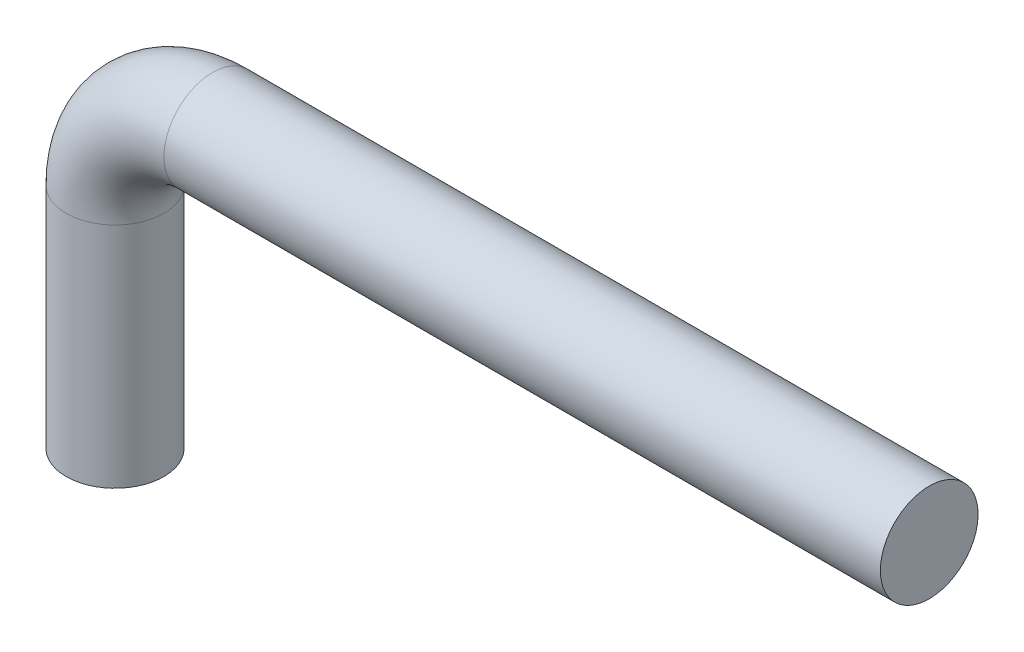
SolidWorks part; units mm, degrees
ref_plane "Front Plane" through (0, 0, 0) normal (0, 0, 1) x (1, 0, 0)
ref_plane "Top Plane" through (0, 0, 0) normal (0, 1, 0) x (1, 0, 0)
ref_plane "Right Plane" through (0, 0, 0) normal (1, 0, 0) x (0, 0, -1)
sketch "Sketch1" plane through (0, 0, 0) normal (0, 0, 1) x (1, 0, 0)
  line L0 (42.1927, 25.9485) -> (-13.6873, 25.9485)
  line L1 (-21.3073, 18.3285) -> (-21.3073, 0.5485)
  arc A0 (-21.3073, 18.3285) -> (-13.6873, 25.9485) centre (-13.6873, 18.3285) cw
  point P5 (-21.3073, 25.9485)
  dimension "D3" = 7.62
  dimension "D1" = 63.5
  dimension "D2" = 25.4
sweep "Sweep1" add path "Sketch1" circular profile diameter 7.62 parameters "D3"=7.62
